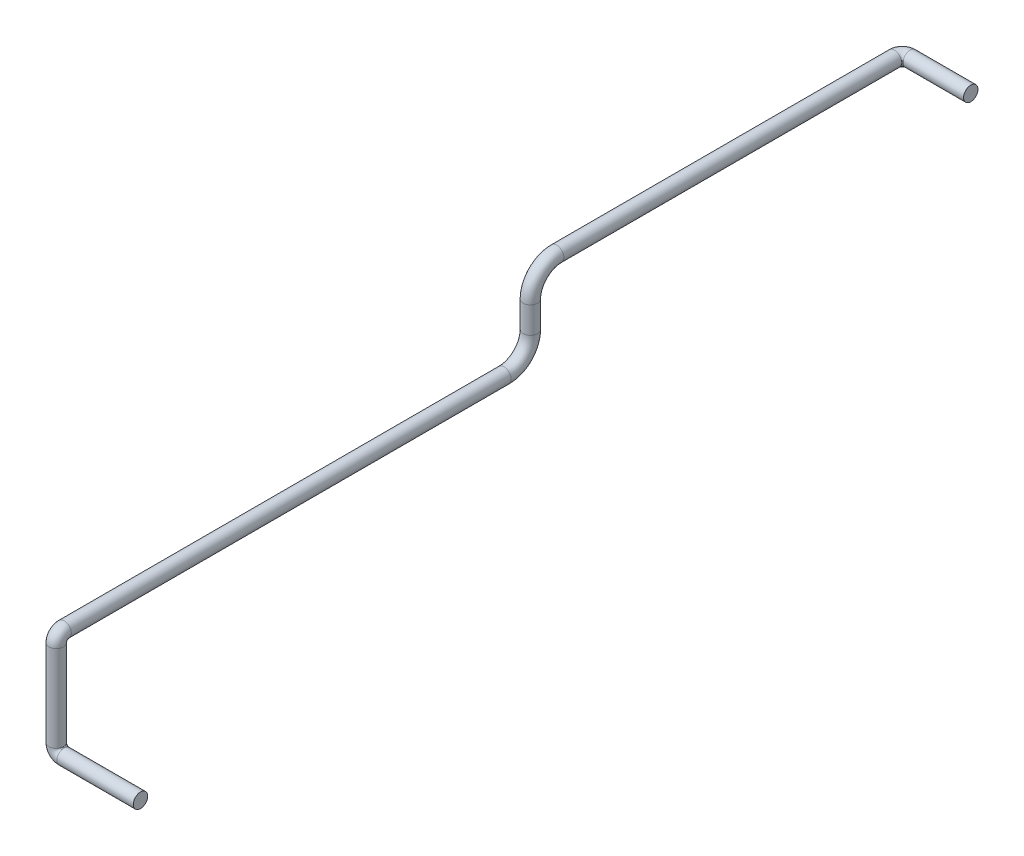
SolidWorks part; units mm, degrees
ref_plane "Alzado" through (0, 0, 0) normal (0, 0, 1) x (1, 0, 0)
ref_plane "Planta" through (0, 0, 0) normal (0, 1, 0) x (1, 0, 0)
ref_plane "Vista lateral" through (0, 0, 0) normal (1, 0, 0) x (0, 0, -1)
sketch3d "Croquis3D1"
  line L0 (0, 0, 0) -> (-145, 0, 0)
  line L1 (-160, 15, 0) -> (-160, 179, 0)
  line L2 (-160, 344, -950) -> (-160, 344, -1591)
  line L3 (-145, 344, -1606) -> (-30, 344, -1606)
  line L4 (-160, 194, -15) -> (-160, 194, -850)
  line L5 (-160, 294, -900) -> (-160, 244, -900)
  arc A0 (-160, 194, -15) -> (-160, 179, 0) centre (-160, 179, -15) ccw
  arc A1 (-145, 0, 0) -> (-160, 15, 0) centre (-145, 15, 0) ccw
  arc A2 (-160, 294, -900) -> (-160, 344, -950) centre (-160, 294, -950) ccw
  arc A3 (-160, 244, -900) -> (-160, 194, -850) centre (-160, 244, -850) ccw
  arc A4 (-160, 344, -1591) -> (-145, 344, -1606) centre (-145, 344, -1591) ccw
  point P10 (-160, 194, 0)
  point P11 (-145, 179, -15)
  point P14 (-160, 0, 0)
  point P15 (-145, 15, -15)
  point P18 (-160, 344, -900)
  point P19 (-210, 294, -950)
  point P22 (-160, 194, -900)
  point P23 (-210, 244, -850)
  point P26 (-160, 344, -1606)
  point P27 (-145, 329, -1591)
  dimension "D6" = 15
  dimension "D7" = 50
  dimension "D8" = 15
  dimension "D1" = 160
  dimension "D2" = 194
  dimension "D5" = 706
  dimension "D3" = 900
  dimension "D4" = 130
  dimension "D9" = 150
sketch "Croquis1" plane through (0, 0, 0) normal (1, 0, 0) x (0, 0, -1)
  circle A0 centre (0, 0) radius 13.7
  dimension "D1" = 27.4
sweep "Barrer1" add profiles "Croquis1" path "Croquis3D1"
